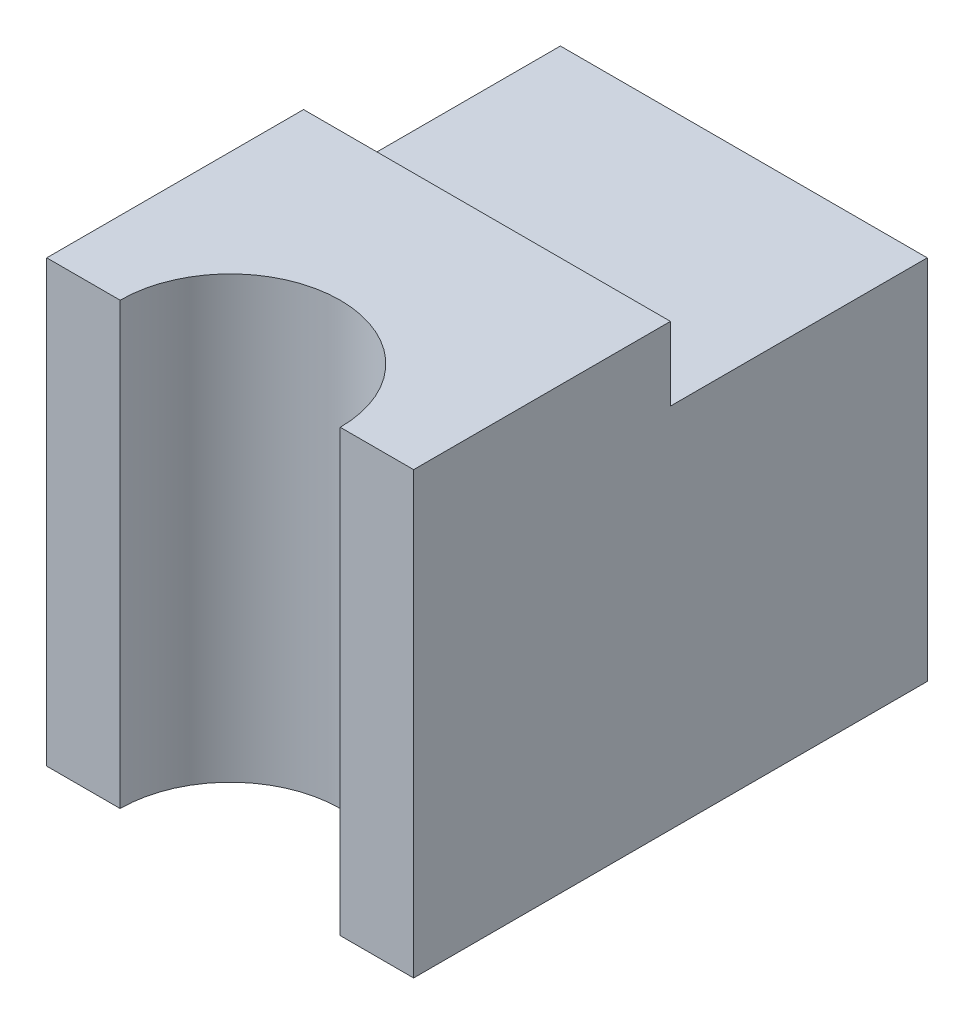
SolidWorks part; units mm, degrees
ref_plane "Front Plane" through (0, 0, 0) normal (0, 0, 1) x (1, 0, 0)
ref_plane "Top Plane" through (0, 0, 0) normal (0, 1, 0) x (1, 0, 0)
ref_plane "Right Plane" through (0, 0, 0) normal (1, 0, 0) x (0, 0, -1)
sketch "Sketch1" plane through (0, 0, 0) normal (0, 1, 0) x (1, 0, 0)
  line L1 (0, 0) -> (0.5, 0)
  line L2 (0, 0) -> (0, 0.7)
  line L3 (0, 0.7) -> (0.5, 0.7)
  line L4 (0.5, 0) -> (0.5, 0.7)
extrude "Boss-Extrude1" add sketch "Sketch1" along normal blind 0.6
sketch "Sketch2" plane through (0, 0.6, 0) normal (0, 1, 0) x (1, 0, 0)
  line L0 (0, 0) -> (0.5, 0) construction
  circle A0 centre (0.25, 0) radius 0.15
extrude "Cut-Extrude1" cut sketch "Sketch2" against normal up to next
sketch "Sketch3" plane through (0, 0.6, 0) normal (0, 1, 0) x (1, 0, 0)
  line L0 (0, 0.7) -> (0, 0) construction
  line L1 (0.5, 0.7) -> (0, 0.7)
  line L2 (0.5, 0.7) -> (0.5, 0.35)
  line L3 (0.5, 0.35) -> (0, 0.35)
  line L4 (0, 0.7) -> (0, 0.35)
extrude "Cut-Extrude2" cut sketch "Sketch3" against normal blind 0.1
